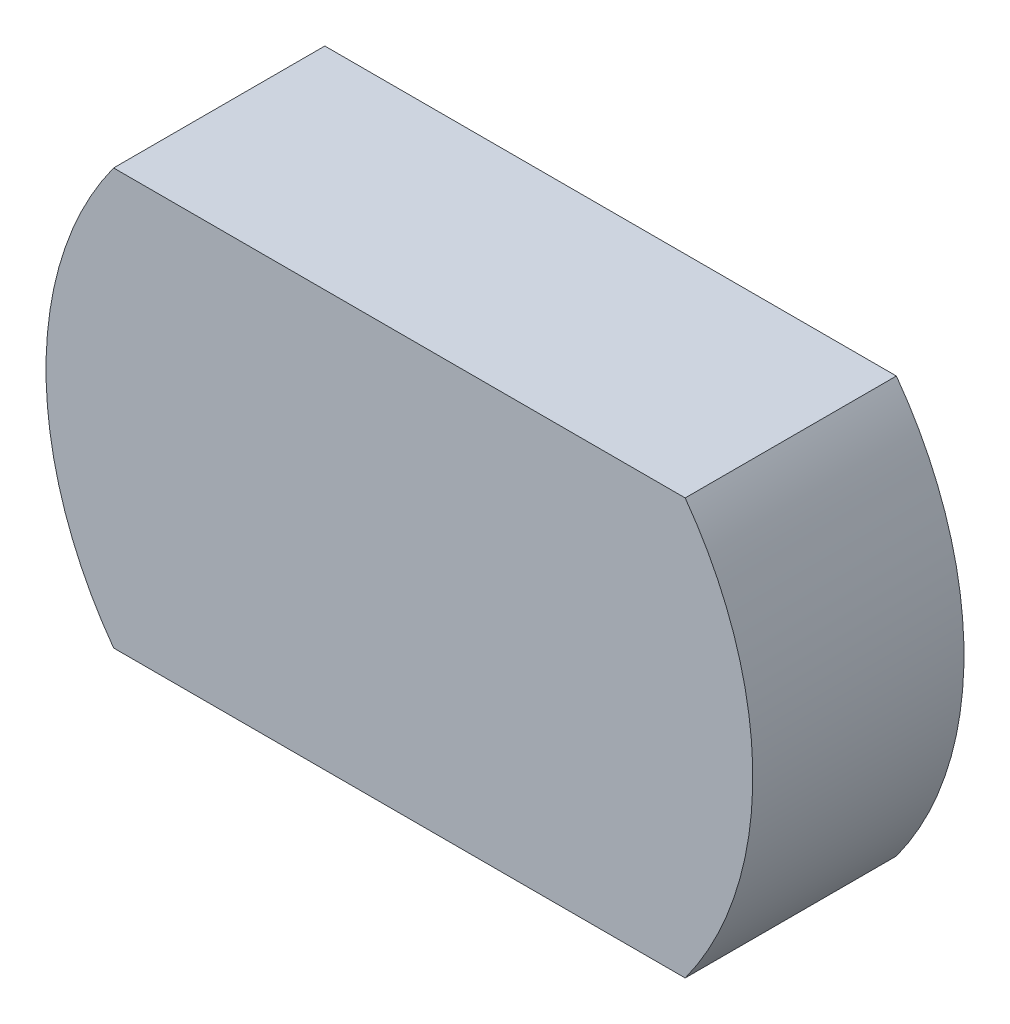
SolidWorks part; units mm, degrees
ref_plane "Front Plane" through (0, 0, 0) normal (0, 0, 1) x (1, 0, 0)
ref_plane "Top Plane" through (0, 0, 0) normal (0, 1, 0) x (1, 0, 0)
ref_plane "Right Plane" through (0, 0, 0) normal (1, 0, 0) x (0, 0, -1)
sketch "Sketch1" plane through (0, 0, 0) normal (0, 0, 1) x (1, 0, 0)
  line L0 (-73.039, 0) -> (73.039, 0) construction
  line L1 (-73.039, -25) -> (73.039, -25)
  line L2 (-73.039, 25) -> (73.039, 25)
  circle A0 centre (0, 0) radius 30
  circle A1 centre (-30, 0) radius 4
  circle A2 centre (30, 0) radius 4
  circle A3 centre (0, 0) radius 42.5
  circle A4 centre (0, 0) radius 17.5
  dimension "D1" = 60
  dimension "D2" = 8
  dimension "D3" = 85
  dimension "D6" = 35
  dimension "D4" = 25
  dimension "D5" = 25
sketch "Sketch2" plane through (0, 0, 0) normal (0, 0, 1) x (1, 0, 0)
  line L0 (-73.039, 25) -> (73.039, 25) construction
  line L1 (-73.039, -25) -> (73.039, -25) construction
  line L2 (-34.3693, 25) -> (34.3693, 25)
  line L3 (-34.3693, -25) -> (34.3693, -25)
  arc A0 (34.3693, -25) -> (34.3693, 25) centre (0, 0) ccw
  circle A1 centre (0, 0) radius 42.5
  arc A2 (-34.3693, 25) -> (-34.3693, -25) centre (0, 0) ccw
  dimension "D1" = 0
extrude "Boss-Extrude1" [suppressed] add sketch "Sketch2" along normal blind 15
sketch "Sketch3" plane through (0, 0, 0) normal (0, 0, 1) x (1, 0, 0)
  line L0 (17.5, 17.8536) -> (17.5, 42.5593)
  line L5 (17.5, -42.5593) -> (-17.5, -42.5593)
  line L6 (17.5, -42.5593) -> (17.5, -17.8536)
  line L7 (17.5, 42.5593) -> (-17.5, 42.5593)
  line L8 (-17.5, -42.5593) -> (-17.5, -17.8536)
  line L9 (17.5, -42.5593) -> (-17.5, 42.5593) construction
  line L10 (17.5, 42.5593) -> (-17.5, -42.5593) construction
  line L11 (-17.5, 17.8536) -> (-17.5, 42.5593)
  arc A0 (-17.5, 17.8536) -> (-17.5, -17.8536) centre (0, 0) ccw
  arc A3 (17.5, -17.8536) -> (17.5, 17.8536) centre (0, 0) ccw
  dimension "D1" = 50
  dimension "D2" = 35
extrude "Cut-Extrude1" [suppressed] cut sketch "Sketch3" along normal blind 10
fillet "Fillet1" [suppressed] radius 1
fillet "Fillet2" [suppressed] radius 1
sketch "Sketch4" [suppressed] plane through (0, 0, 15) normal (0, 0, 1) x (1, 0, 0)
  circle A0 centre (-30, 0) radius 4 construction
  circle A1 centre (30, 0) radius 4 construction
  circle A2 centre (-30, 0) radius 4
  circle A3 centre (30, 0) radius 4
extrude "Cut-Extrude2" [suppressed] cut sketch "Sketch4" against normal offset from surface (14 mm away) 1
fillet "Fillet3" [suppressed] radius 2
sketch "Sketch5" plane through (0, 0, 0) normal (0, 0, 1) x (1, 0, 0)
  line L0 (-73.039, 25) -> (73.039, 25) construction
  line L1 (-73.039, -25) -> (73.039, -25) construction
  line L2 (-34.3693, 25) -> (34.3693, 25)
  line L3 (-34.3693, -25) -> (34.3693, -25)
  arc A0 (34.3693, -25) -> (34.3693, 25) centre (0, 0) ccw
  circle A1 centre (0, 0) radius 42.5
  arc A2 (-34.3693, 25) -> (-34.3693, -25) centre (0, 0) ccw
  dimension "D1" = 0
extrude "Boss-Extrude2" add sketch "Sketch5" along normal blind 25.4
